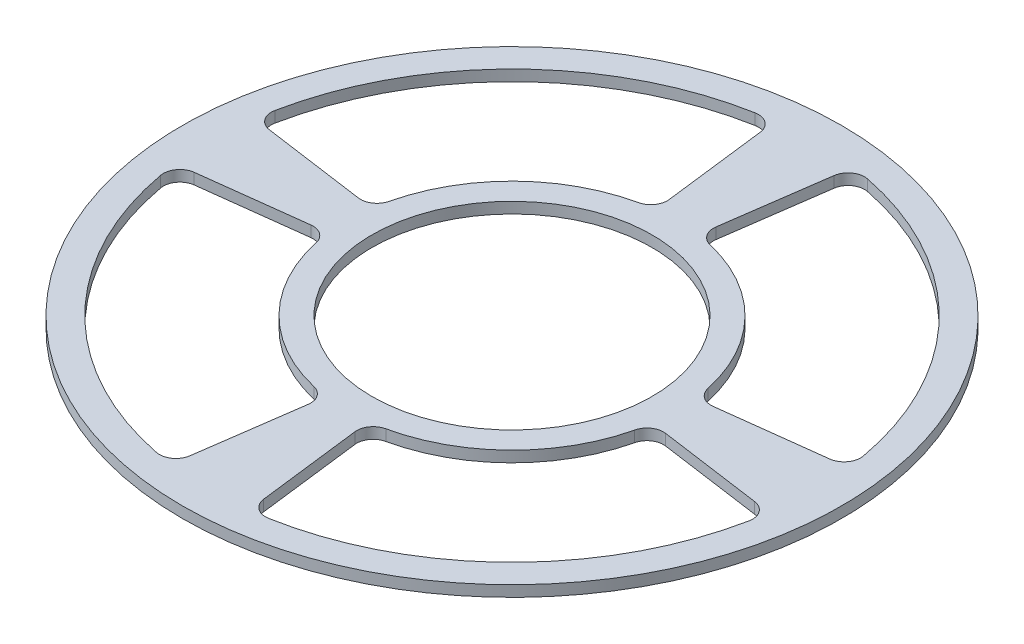
SolidWorks part; units mm, degrees
material "A-Glass Fiber"
ref_plane "Front Plane" through (0, 0, 0) normal (0, 0, 1) x (1, 0, 0)
ref_plane "Top Plane" through (0, 0, 0) normal (0, 1, 0) x (1, 0, 0)
ref_plane "Right Plane" through (0, 0, 0) normal (1, 0, 0) x (0, 0, -1)
sketch "Sketch1" plane through (0, 0, 0) normal (0, 1, 0) x (1, 0, 0)
  circle A0 centre (0, 0) radius 60
  circle A1 centre (0, 0) radius 25.5
  point P15 (0, 0)
  dimension "D1" = 51
  dimension "D2" = 120
extrude "Boss-Extrude1" add sketch "Sketch1" along normal blind 2
sketch "Sketch2" plane through (0, 2, 0) normal (0, 1, 0) x (1, 0, 0)
  line L0 (-32.6184, -4.005) -> (-51.5264, -6.3267)
  line L1 (-4.5737, -32.5435) -> (-7.2249, -51.4082)
  line L2 (-29.7764, -3.6561) -> (0, 0) construction
  line L3 (0, 0) -> (-4.1752, -29.708) construction
  arc A0 (-54.1124, -9.8411) -> (-10.784, -53.9324) centre (0, 0) ccw
  arc A1 (-29.3207, -6.3479) -> (-6.8586, -29.2055) centre (0, 0) ccw
  arc A6 (-10.784, -53.9324) -> (-7.2249, -51.4082) centre (-10.1958, -50.9907) ccw
  arc A7 (-6.8586, -29.2055) -> (-4.5737, -32.5435) centre (-7.5445, -32.126) cw
  arc A8 (-29.3207, -6.3479) -> (-32.6184, -4.005) centre (-32.2528, -6.9827) ccw
  arc A9 (-54.1124, -9.8411) -> (-51.5264, -6.3267) centre (-51.1608, -9.3043) cw
  dimension "D1" = 30
  dimension "D2" = 55
  dimension "D5" = 3
  dimension "D3" = 75
extrude "Cut-Extrude1" cut sketch "Sketch2" against normal up to surface (2 mm away) up to face at (0, 0, 60)
pattern_circular "CirPattern1" count 4 over 360 about axis through (0, 0, 0) along (0, 1, 0) of "Cut-Extrude1"
